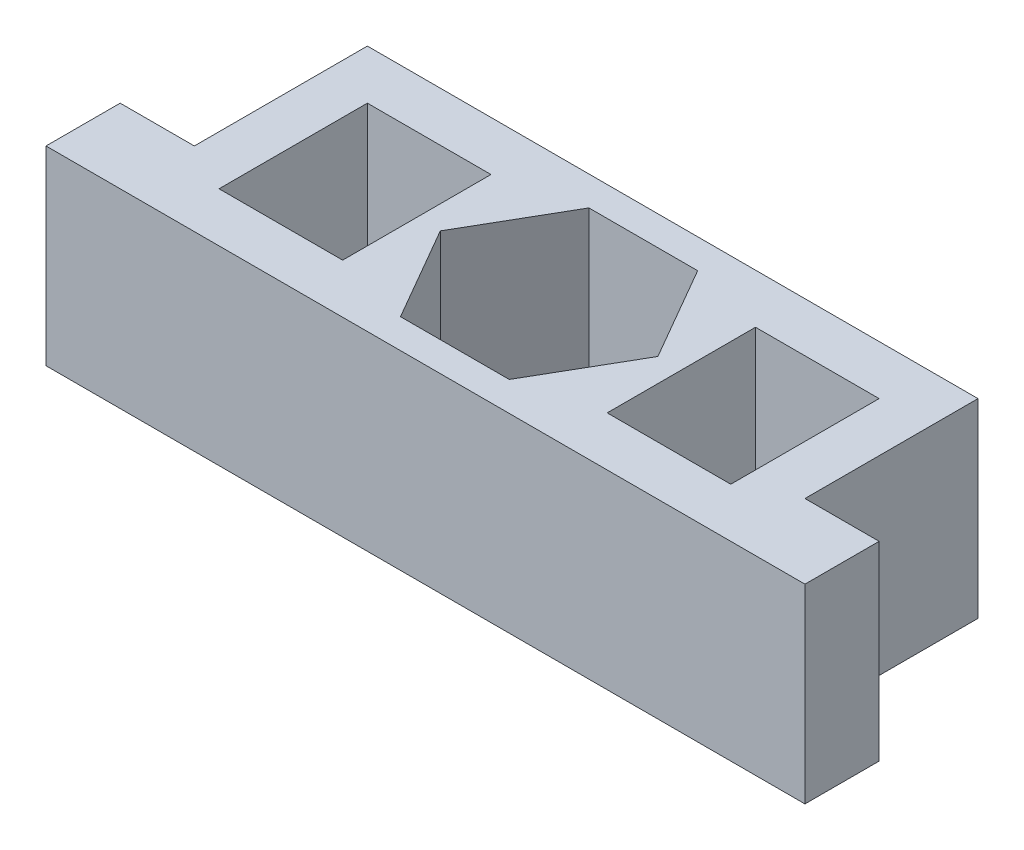
SolidWorks part; units mm, degrees
ref_plane "Plan de face" through (0, 0, 0) normal (0, 0, 1) x (1, 0, 0)
ref_plane "Plan de dessus" through (0, 0, 0) normal (0, 1, 0) x (1, 0, 0)
ref_plane "Plan de droite" through (0, 0, 0) normal (1, 0, 0) x (0, 0, -1)
sketch "Sketch1" plane through (0, 0, 0) normal (0, 0, 1) x (1, 0, 0)
  line L1 (-12.35, 3.85) -> (12.35, 3.85)
  line L2 (-12.35, 3.85) -> (-12.35, -3.85)
  line L3 (-12.35, -3.85) -> (12.35, -3.85)
  line L4 (12.35, 3.85) -> (12.35, -3.85)
  line L5 (-12.35, 3.85) -> (12.35, -3.85) construction
  line L6 (-12.35, -3.85) -> (12.35, 3.85) construction
  point P0 (0, 0)
  dimension "D1" = 24.7
  dimension "D2" = 7.7
extrude "Boss-Extrude1" add sketch "Sketch1" along normal blind 10
sketch "Sketch2" plane through (0, -3.85, 0) normal (0, -1, 0) x (1, 0, 0)
  line L0 (-12.35, 10) -> (12.35, 0) construction
  line L2 (12.35, 10) -> (-12.35, 0) construction
  line L3 (-12.35, 0) -> (12.35, 0) construction
  line L4 (-12.35, 10) -> (-12.35, 0) construction
  line L5 (4.4, 5) -> (2.2, 8.8105)
  line L6 (2.2, 8.8105) -> (-2.2, 8.8105)
  line L7 (-2.2, 8.8105) -> (-4.4, 5)
  line L8 (-4.4, 5) -> (-2.2, 1.1895)
  line L9 (-2.2, 1.1895) -> (2.2, 1.1895)
  line L10 (2.2, 1.1895) -> (4.4, 5)
  circle A0 centre (0, 5) radius 3.8105 construction
  dimension "D1" = 8.8
extrude "Cut-Extrude1" cut sketch "Sketch2" against normal blind 10
sketch "Sketch3" plane through (0, 3.85, 0) normal (0, 1, 0) x (1, 0, 0)
  line L0 (-12.35, -10) -> (-12.35, 0) construction
  line L7 (-5.35, -2) -> (-5.35, -8)
  line L8 (-10.35, -2) -> (-5.35, -2)
  line L13 (-10.35, -2) -> (-10.35, -8)
  line L14 (-10.35, -8) -> (-5.35, -8)
  line L17 (12.35, 0) -> (-12.35, 0) construction
  line L18 (12.35, -10) -> (-12.35, -10) construction
  point P5 (0, -5)
  point P6 (0, -5)
  point P10 (0, -5)
  dimension "D1" = 2
  dimension "D2" = 2
  dimension "D3" = 2
  dimension "D4" = 5
extrude "Cut-Extrude2" cut sketch "Sketch3" against normal blind 10
mirror "Mirror1" about plane through (0, 0, 0) normal (1, 0, 0) of "Cut-Extrude2"
sketch "Sketch4" plane through (12.35, 0, 0) normal (1, 0, 0) x (0, 0, -1)
  line L5 (-10, -3.85) -> (0, -3.85) construction
  line L6 (-10, 3.85) -> (-7, 3.85)
  line L7 (-10, 3.85) -> (-10, -3.85)
  line L8 (-10, -3.85) -> (-7, -3.85)
  line L9 (-7, 3.85) -> (-7, -3.85)
  dimension "D1" = 3
extrude "Boss-Extrude2" add sketch "Sketch4" along normal blind 3
mirror "Mirror2" about plane through (0, 0, 0) normal (1, 0, 0) of "Boss-Extrude2"
